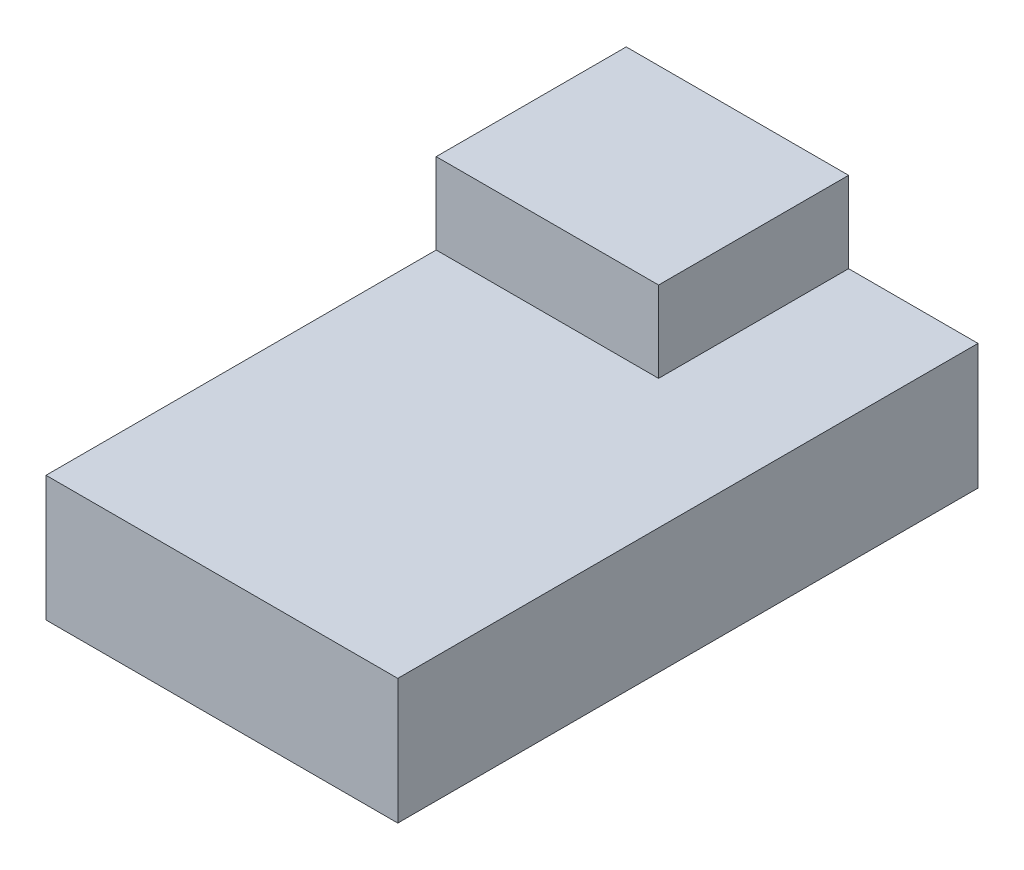
SolidWorks part; units mm, degrees
material "Custom Plastic"
ref_plane "Front Plane" through (0, 0, 0) normal (0, 0, 1) x (1, 0, 0)
ref_plane "Top Plane" through (0, 0, 0) normal (0, 1, 0) x (1, 0, 0)
ref_plane "Right Plane" through (0, 0, 0) normal (1, 0, 0) x (0, 0, -1)
sketch "Sketch1" plane through (0, 0, 0) normal (0, 1, 0) x (1, 0, 0)
  line L1 (11.049, -18.2244) -> (-11.049, -18.2244)
  line L2 (11.049, -18.2244) -> (11.049, 18.2244)
  line L3 (11.049, 18.2244) -> (-11.049, 18.2244)
  line L4 (-11.049, -18.2244) -> (-11.049, 18.2244)
  line L5 (11.049, -18.2244) -> (-11.049, 18.2244) construction
  line L6 (11.049, 18.2244) -> (-11.049, -18.2244) construction
  point P0 (0, 0)
extrude "Extrude1" add sketch "Sketch1" along normal blind 7.874
sketch "Sketch2" plane through (0, 7.874, 0) normal (0, 1, 0) x (-1, 0, 0)
  line L0 (11.049, -18.2244) -> (-2.921, -18.2244) construction
  line L1 (-11.049, -18.2244) -> (11.049, -18.2244) construction
  line L2 (-2.921, -18.2244) -> (-2.921, -6.2864) construction
  line L4 (11.049, -18.2244) -> (-2.921, -18.2244)
  line L5 (11.049, -18.2244) -> (11.049, -6.2864)
  line L6 (11.049, -6.2864) -> (-2.921, -6.2864)
  line L7 (-2.921, -18.2244) -> (-2.921, -6.2864)
extrude "Extrude2" add sketch "Sketch2" along normal blind 5.08
